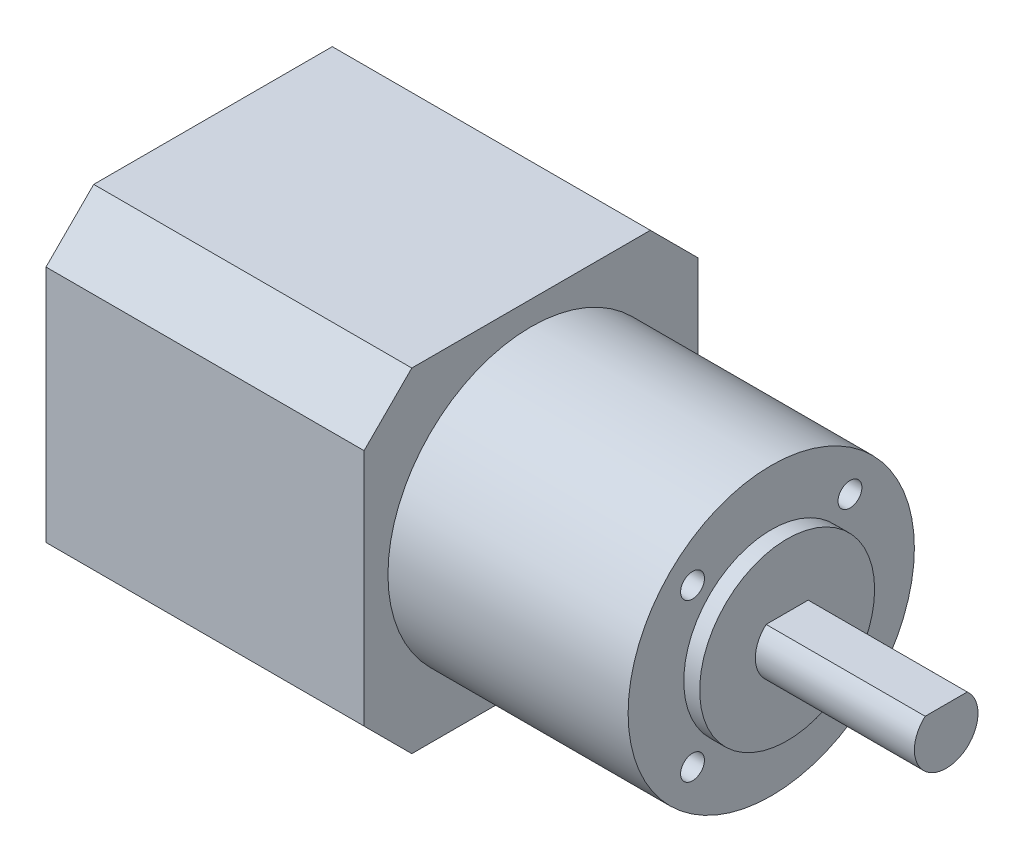
SolidWorks part; units mm, degrees
ref_plane "Front Plane" through (0, 0, 0) normal (0, 0, 1) x (1, 0, 0)
ref_plane "Top Plane" through (0, 0, 0) normal (0, 1, 0) x (1, 0, 0)
ref_plane "Right Plane" through (0, 0, 0) normal (1, 0, 0) x (0, 0, -1)
sketch "Sketch1" plane through (0, 0, 0) normal (1, 0, 0) x (0, 0, -1)
  line L0 (-21, 15) -> (-15, 21)
  line L1 (-15, -21) -> (15, -21)
  line L2 (-21, -15) -> (-21, 15)
  line L3 (-15, 21) -> (15, 21)
  line L4 (21, -15) -> (21, 15)
  line L5 (-21, -21) -> (21, 21) construction
  line L6 (-21, 21) -> (21, -21) construction
  line L7 (15, 21) -> (21, 15)
  line L8 (15, -21) -> (21, -15)
  line L9 (-21, -15) -> (-15, -21)
  point P0 (0, 0)
  dimension "D1" = 42
  dimension "D2" = 42
extrude "Boss-Extrude1" add sketch "Sketch1" along normal blind 40
sketch "Sketch2" plane through (40, 0, 0) normal (1, 0, 0) x (0, 0, -1)
  line L0 (0, 0) -> (24.4009, -24.4009) construction
  line L3 (-15, 21) -> (-21, 15) construction
  circle A0 centre (0, 0) radius 18
  circle A1 centre (0, 0) radius 14 construction
  circle A2 centre (-9.8995, 9.8995) radius 1.5
  circle A3 centre (9.8995, 9.8995) radius 1.5
  circle A4 centre (9.8995, -9.8995) radius 1.5
  circle A5 centre (-9.8995, -9.8995) radius 1.5
  point P13 (-18, 18)
  dimension "D1" = 36
  dimension "D2" = 28
  dimension "D3" = 3
  dimension "D4" = 4
extrude "Boss-Extrude2" add sketch "Sketch2" along normal blind 30.2
sketch "Sketch3" plane through (70.2, 0, 0) normal (1, 0, 0) x (0, 0, -1)
  circle A0 centre (0, 0) radius 11
  dimension "D1" = 22
extrude "Boss-Extrude3" add sketch "Sketch3" along normal blind 2
sketch "Sketch4" plane through (72.2, 0, 0) normal (1, 0, 0) x (0, 0, -1)
  line L0 (2.6458, 3) -> (-2.6458, 3)
  arc A0 (-2.6458, 3) -> (2.6458, 3) centre (0, 0) ccw
  dimension "D1" = 8
  dimension "D2" = 3
extrude "Boss-Extrude4" add sketch "Sketch4" along normal blind 20
